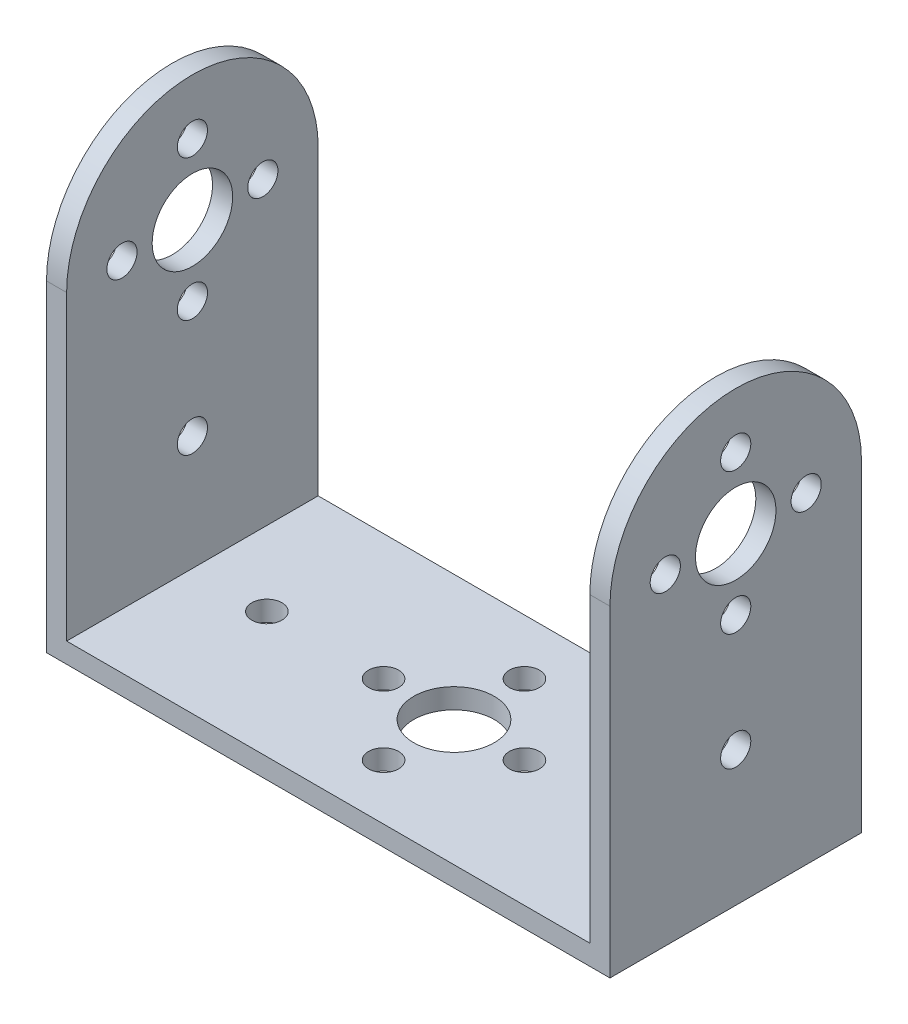
SolidWorks part; units mm, degrees
material "5052-H32"
ref_plane "Front Plane" through (0, 0, 0) normal (0, 0, 1) x (1, 0, 0)
ref_plane "Top Plane" through (0, 0, 0) normal (0, 1, 0) x (1, 0, 0)
ref_plane "Right Plane" through (0, 0, 0) normal (1, 0, 0) x (0, 0, -1)
sketch "Sketch1" plane through (0, 0, 0) normal (0, 1, 0) x (1, 0, 0)
  line L1 (26, -12.5) -> (-26, -12.5)
  line L2 (26, -12.5) -> (26, 12.5)
  line L3 (26, 12.5) -> (-26, 12.5)
  line L4 (-26, -12.5) -> (-26, 12.5)
  line L5 (26, -12.5) -> (-26, 12.5) construction
  line L6 (26, 12.5) -> (-26, -12.5) construction
  point P0 (0, 0)
  dimension "D1" = 52
  dimension "D2" = 25
extrude "Boss-Extrude1" add sketch "Sketch1" along normal blind 2
sketch "Sketch3" plane through (0, 2, 0) normal (0, 1, 0) x (1, 0, 0)
  circle A0 centre (0, 0) radius 4
  circle A1 centre (18.6, 0) radius 1.5
  circle A2 centre (7, 0) radius 1.5
  circle A3 centre (0, 7) radius 1.5
  circle A4 centre (-7, 0) radius 1.5
  circle A5 centre (0, -7) radius 1.5
  circle A6 centre (-18.6, 0) radius 1.5
  dimension "D1" = 3
  dimension "D2" = 8
  dimension "D3" = 3
  dimension "D4" = 3
  dimension "D5" = 3
  dimension "D6" = 3
  dimension "D7" = 3
  dimension "D8" = 18.6
  dimension "D9" = 18.6
extrude "Cut-Extrude1" cut sketch "Sketch3" against normal through all
sketch "Sketch4" plane through (26, 0, 0) normal (1, 0, 0) x (0, 0, -1)
  line L1 (-12.5, 0) -> (12.5, 0)
  line L2 (-12.5, 0) -> (-12.5, 32)
  line L4 (12.5, 0) -> (12.5, 32)
  arc A0 (-12.5, 32) -> (12.5, 32) centre (0, 32) cw
  circle A1 centre (0, 32) radius 4
  circle A3 centre (0, 39) radius 1.5
  circle A4 centre (7, 32) radius 1.5
  circle A5 centre (0, 25) radius 1.5
  circle A6 centre (-7, 32) radius 1.5
  circle A7 centre (0, 13.4) radius 1.5
  dimension "D3" = 3
  dimension "D4" = 3
  dimension "D5" = 3
  dimension "D6" = 3
  dimension "D8" = 8
  dimension "D10" = 3
  dimension "D1" = 25
  dimension "D2" = 32
  dimension "D9" = 18.6
extrude "Boss-Extrude3" add sketch "Sketch4" along normal blind 2
sketch "Sketch5" plane through (-26, 0, 0) normal (-1, 0, 0) x (0, 0, 1)
  line L1 (-12.5, 0) -> (12.5, 0)
  line L2 (-12.5, 0) -> (-12.5, 32)
  line L4 (12.5, 0) -> (12.5, 32)
  arc A0 (-12.5, 32) -> (12.5, 32) centre (0, 32) cw
  circle A1 centre (0, 32) radius 4
  circle A2 centre (0, 39) radius 1.4963
  circle A3 centre (7, 32) radius 1.5
  circle A4 centre (0, 25) radius 1.5
  circle A5 centre (-7, 32) radius 1.5
  circle A6 centre (0, 13.4) radius 1.5
  dimension "D1" = 32
  dimension "D2" = 25
extrude "Boss-Extrude4" add sketch "Sketch5" along normal blind 2
